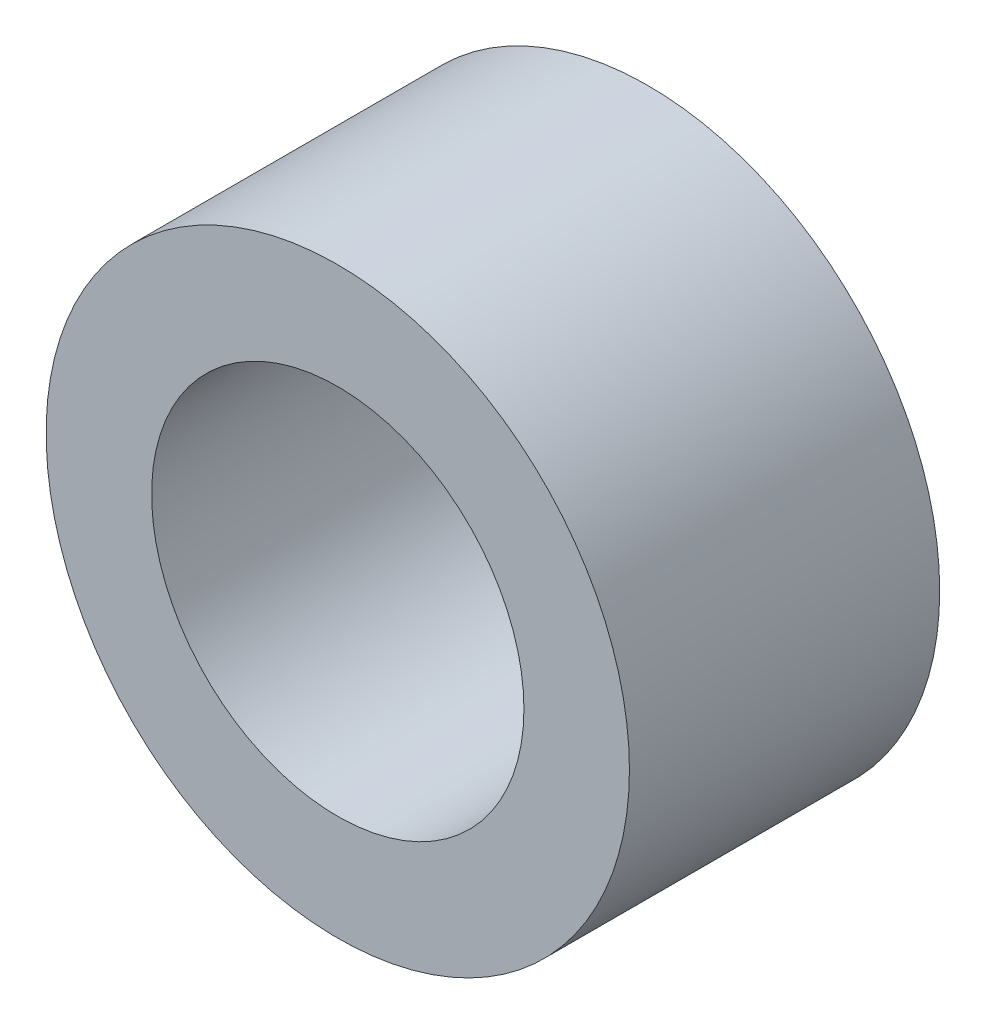
SolidWorks part; units mm, degrees
ref_plane "Front" through (0, 0, 0) normal (0, 0, 1) x (1, 0, 0)
ref_plane "Top" through (0, 0, 0) normal (0, 1, 0) x (1, 0, 0)
ref_plane "Right" through (0, 0, 0) normal (1, 0, 0) x (0, 0, -1)
sketch "Sketch1" plane through (0, 0, 0) normal (0, 0, 1) x (1, 0, 0)
  circle A0 centre (0, 0) radius 3
  circle A1 centre (0, 0) radius 4.7
extrude "Extrude1" add sketch "Sketch1" along normal blind 5
